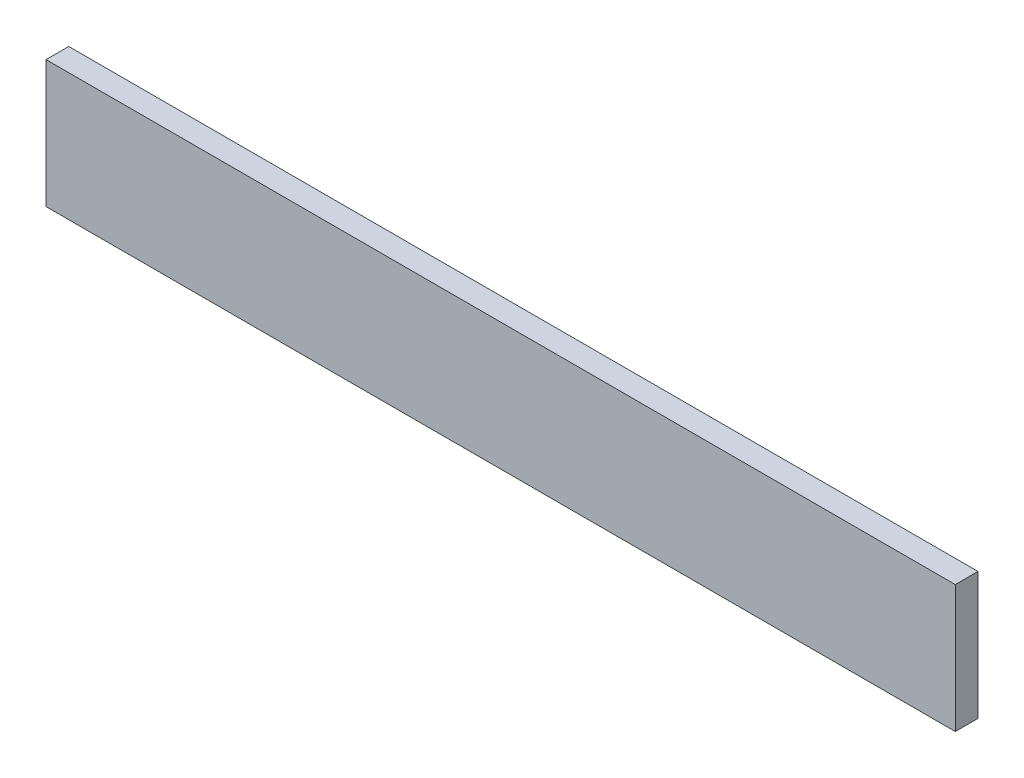
SolidWorks part; units mm, degrees
ref_plane "Front Plane" through (0, 0, 0) normal (0, 0, 1) x (1, 0, 0)
ref_plane "Top Plane" through (0, 0, 0) normal (0, 1, 0) x (1, 0, 0)
ref_plane "Right Plane" through (0, 0, 0) normal (1, 0, 0) x (0, 0, -1)
sketch "Sketch1" plane through (0, 0, 0) normal (0, 0, 1) x (1, 0, 0)
  line L1 (-63.5, -8.89) -> (63.5, -8.89)
  line L2 (-63.5, -8.89) -> (-63.5, 8.89)
  line L3 (-63.5, 8.89) -> (63.5, 8.89)
  line L4 (63.5, -8.89) -> (63.5, 8.89)
  line L5 (-63.5, -8.89) -> (63.5, 8.89) construction
  line L6 (-63.5, 8.89) -> (63.5, -8.89) construction
  point P0 (0, 0)
  dimension "D1" = 127
  dimension "D2" = 17.78
extrude "Boss-Extrude1" add sketch "Sketch1" along normal blind 3.175
